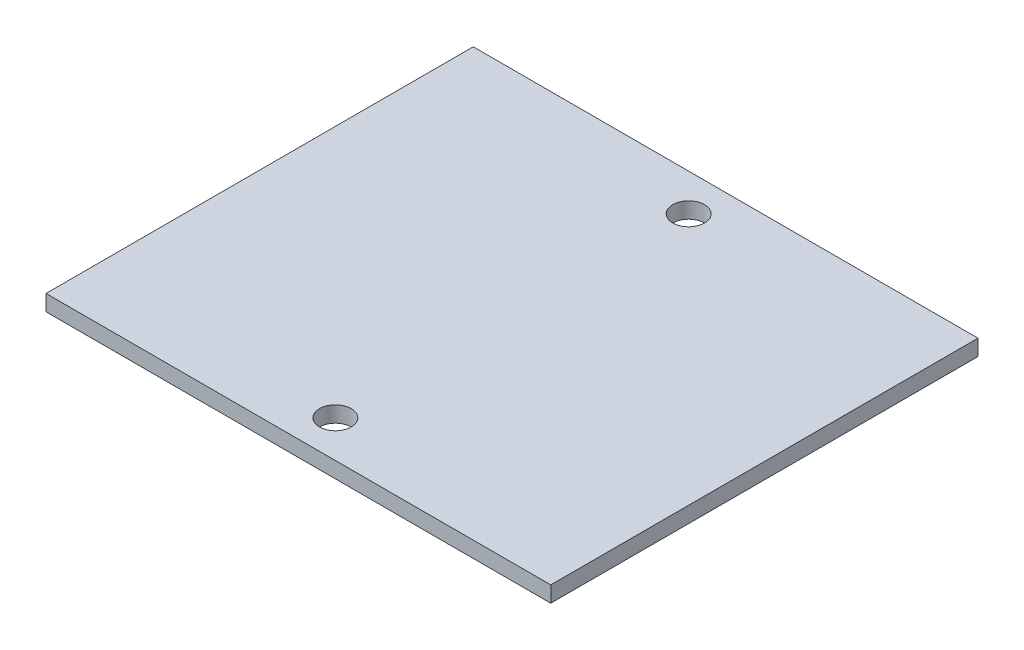
SolidWorks part; units mm, degrees
ref_plane "Front Plane" through (0, 0, 0) normal (0, 0, 1) x (1, 0, 0)
ref_plane "Top Plane" through (0, 0, 0) normal (0, 1, 0) x (1, 0, 0)
ref_plane "Right Plane" through (0, 0, 0) normal (1, 0, 0) x (0, 0, -1)
sketch "Sketch1" plane through (0, 0, 0) normal (0, 1, 0) x (1, 0, 0)
  line L1 (0, 0) -> (50.8, 0)
  line L2 (0, 0) -> (0, 43)
  line L3 (0, 43) -> (50.8, 43)
  line L4 (50.8, 0) -> (50.8, 43)
  circle A2 centre (25.4, 39.28) radius 1.6
  circle A3 centre (25.4, 3.72) radius 1.6
  point P12 (25.4, 43)
  dimension "D3" = 3.72
  dimension "D2" = 35.56
  dimension "D4" = 3.2
  dimension "D1" = 43
  dimension "50.8" = 50.8
extrude "Boss-Extrude1" add sketch "Sketch1" along normal blind 1.6002
